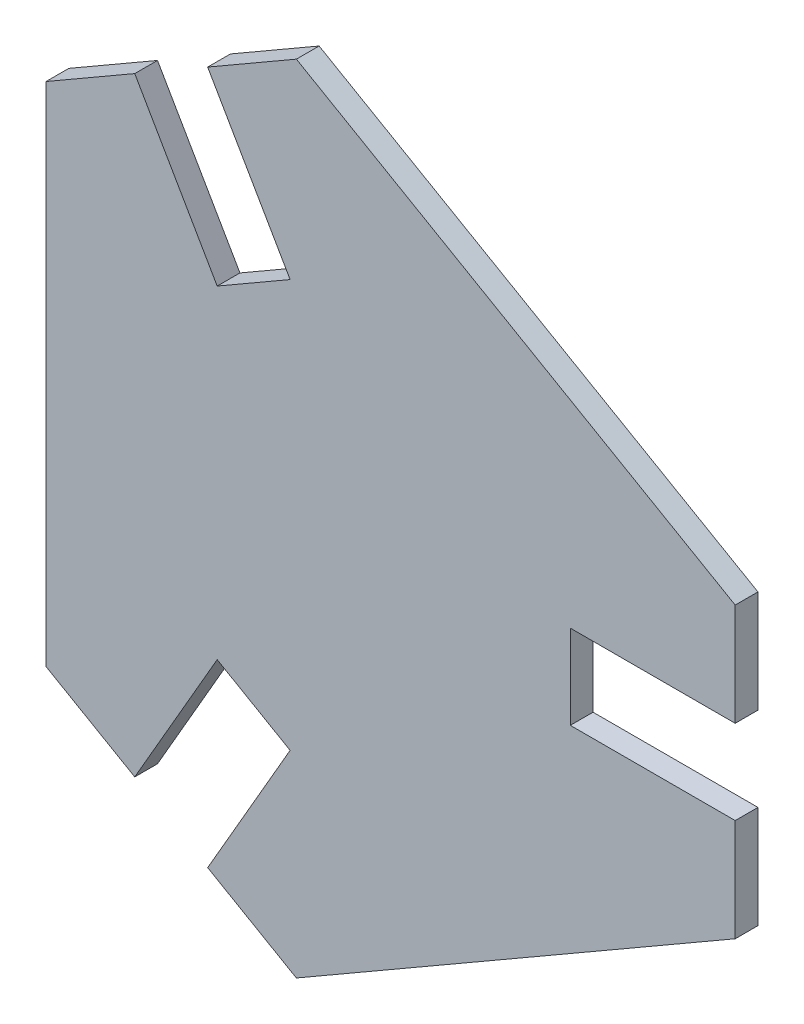
SolidWorks part; units mm, degrees
ref_plane "Alzado" through (0, 0, 0) normal (0, 0, 1) x (1, 0, 0)
ref_plane "Planta" through (0, 0, 0) normal (0, 1, 0) x (1, 0, 0)
ref_plane "Vista lateral" through (0, 0, 0) normal (1, 0, 0) x (0, 0, -1)
sketch "Croquis1" plane through (0, 0, 0) normal (0, 0, 1) x (1, 0, 0)
  line L0 (0, 0) -> (82.6, 0) construction
  line L1 (82.6, -9.25) -> (46.3758, -9.25)
  line L2 (46.3758, -9.25) -> (46.3758, 9.25)
  line L3 (46.3758, 9.25) -> (82.6, 9.25)
  line L4 (82.6, 9.25) -> (82.6, 31.75)
  line L5 (82.6, -9.25) -> (82.6, -31.75)
  line L6 (-33.2893, -76.1587) -> (-13.8037, -87.4087)
  line L7 (-15.1772, -44.7876) -> (-33.2893, -76.1587)
  line L8 (-31.1986, -35.5376) -> (-15.1772, -44.7876)
  line L9 (-49.3107, -66.9087) -> (-31.1986, -35.5376)
  line L10 (-49.3107, -66.9087) -> (-68.7963, -55.6587)
  line L11 (-49.3107, 66.9087) -> (-68.7963, 55.6587)
  line L12 (-31.1986, 35.5376) -> (-49.3107, 66.9087)
  line L13 (-15.1772, 44.7876) -> (-31.1986, 35.5376)
  line L14 (-33.2893, 76.1587) -> (-15.1772, 44.7876)
  line L15 (-33.2893, 76.1587) -> (-13.8037, 87.4087)
  line L16 (-13.8037, -87.4087) -> (82.6, -31.75)
  line L17 (82.6, 31.75) -> (-13.8037, 87.4087)
  line L18 (-68.7963, 55.6587) -> (-68.7963, -55.6587)
  point P24 (0, 0)
  dimension "D1" = 82.6
  dimension "D2" = 18.5
  dimension "D3" = 9.25
  dimension "D5" = 22.5
  dimension "D6" = 22.5
  dimension "D4" = 3
extrude "Saliente-Extruir1" add sketch "Croquis1" along normal blind 5 contours L18 L10 L9 L8 L7 L6 L16 L5 L1 L2 L3 L4 L17 L15 L14 L13 L12 L11
